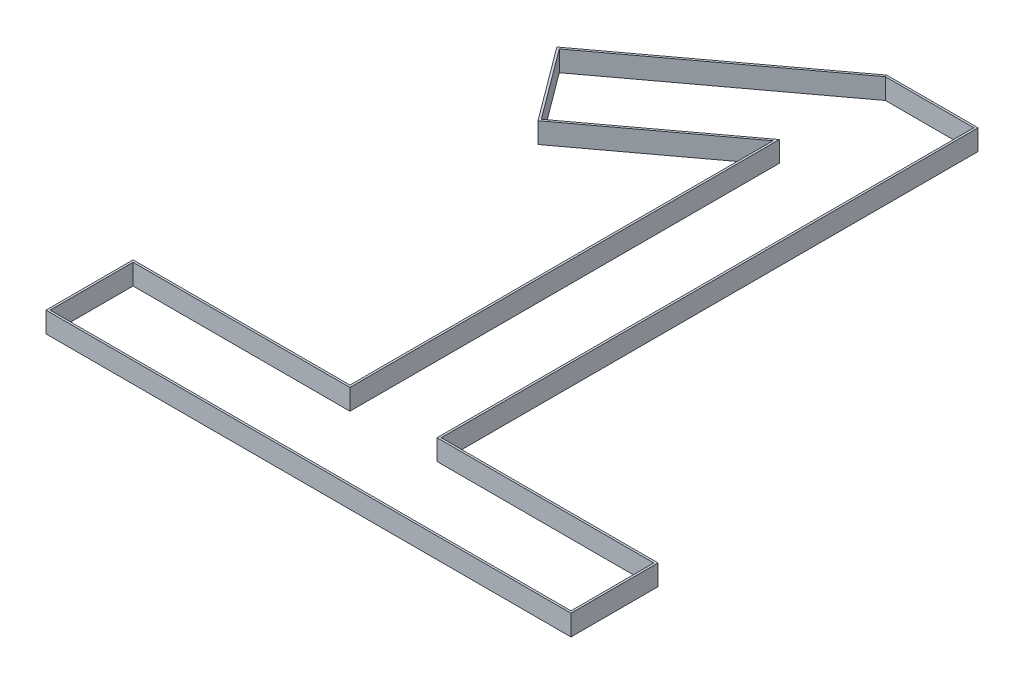
SolidWorks part; units mm, degrees
ref_plane "Front Plane" through (0, 0, 0) normal (0, 0, 1) x (1, 0, 0)
ref_plane "Top Plane" through (0, 0, 0) normal (0, 1, 0) x (1, 0, 0)
ref_plane "Right Plane" through (0, 0, 0) normal (1, 0, 0) x (0, 0, -1)
sketch "Sketch1" plane through (0, 0, 0) normal (0, 1, 0) x (1, 0, 0)
  line L0 (-12.7264, 0) -> (12.7264, 0)
  line L1 (12.7264, 0) -> (12.7264, 4.2216)
  line L2 (12.7264, 4.2216) -> (2.2119, 4.2216)
  line L3 (2.2119, 4.2216) -> (2.2119, 30.2509)
  line L4 (2.2119, 30.2509) -> (-2.2119, 30.2509)
  line L5 (-2.2119, 30.2509) -> (-11.3907, 23.4324)
  line L6 (-11.3907, 23.4324) -> (-8.7526, 19.8812)
  line L7 (-8.7526, 19.8812) -> (-2.2119, 24.7399)
  line L8 (-2.2119, 24.7399) -> (-2.2119, 4.2216)
  line L9 (-2.2119, 4.2216) -> (-12.7264, 4.2216)
  line L10 (-12.7264, 4.2216) -> (-12.7264, 0)
  line L11 (0, 51.1145) -> (0, -20.2529) construction
  line L12 (-2.1789, 30.1509) -> (-11.2508, 23.4118)
  line L13 (-11.2508, 23.4118) -> (-8.732, 20.0211)
  line L14 (-8.732, 20.0211) -> (-2.1119, 24.9388)
  line L15 (-2.1119, 24.9388) -> (-2.1119, 4.1216)
  line L16 (-2.1119, 4.1216) -> (-12.6264, 4.1216)
  line L17 (-12.6264, 4.1216) -> (-12.6264, 0.1)
  line L18 (-12.6264, 0.1) -> (12.6264, 0.1)
  line L19 (12.6264, 0.1) -> (12.6264, 4.1216)
  line L20 (12.6264, 4.1216) -> (2.1119, 4.1216)
  line L21 (2.1119, 4.1216) -> (2.1119, 30.1509)
  line L22 (2.1119, 30.1509) -> (-2.1789, 30.1509)
  point P14 (0, 0)
  point P15 (0, 0)
  dimension "D1" = 0.1
extrude "Boss-Extrude1" add sketch "Sketch1" along normal blind 1
